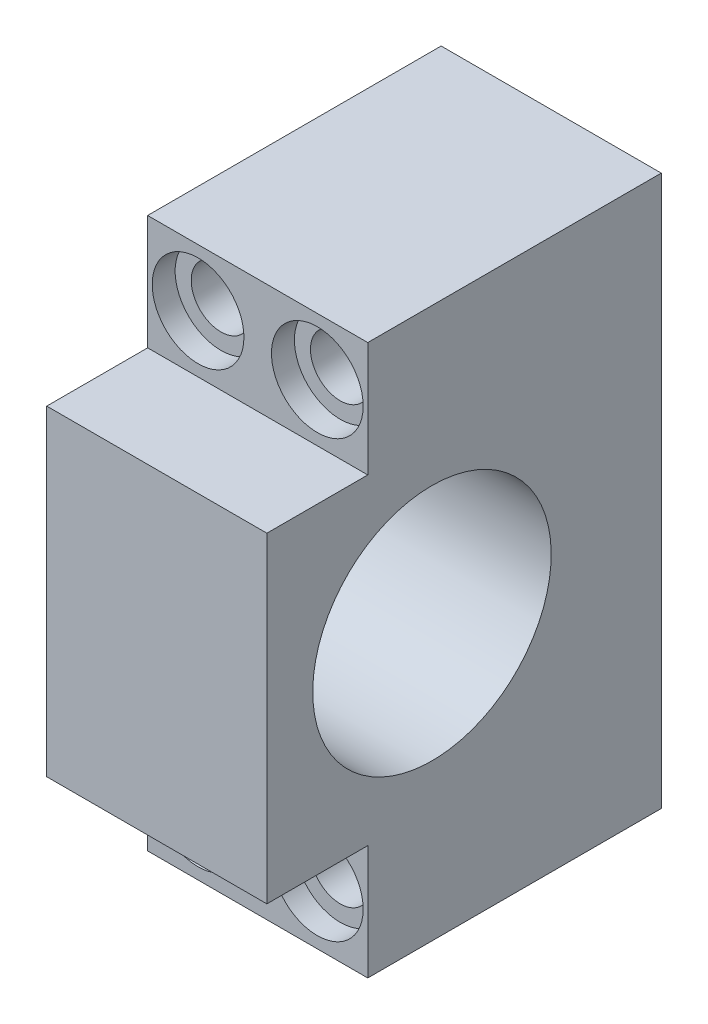
SolidWorks part; units mm, degrees
material "1.0037 (S235JR)"
ref_plane "Front Plane" through (0, 0, 0) normal (0, 0, 1) x (1, 0, 0)
ref_plane "Top Plane" through (0, 0, 0) normal (0, 1, 0) x (1, 0, 0)
ref_plane "Right Plane" through (0, 0, 0) normal (1, 0, 0) x (0, 0, -1)
sketch "Sketch1" plane through (0, 0, 0) normal (0, 0, 1) x (1, 0, 0)
  line L1 (-12, 30) -> (12, 30)
  line L2 (-12, 30) -> (-12, -30)
  line L3 (-12, -30) -> (12, -30)
  line L4 (12, 30) -> (12, -30)
  line L5 (-12, 30) -> (12, -30) construction
  line L6 (-12, -30) -> (12, 30) construction
  point P0 (0, 0)
  dimension "D1" = 24
  dimension "D2" = 60
extrude "Boss-Extrude1" add sketch "Sketch1" along normal blind 43
sketch "Sketch2" plane through (0, 0, 43) normal (0, 0, 1) x (1, 0, 0)
  line L0 (12, -30) -> (12, 30) construction
  line L1 (-12, -30) -> (12, -30)
  line L2 (-12, -30) -> (-12, -17.5)
  line L3 (-12, -17.5) -> (12, -17.5)
  line L4 (12, -30) -> (12, -17.5)
  line L6 (-12, 30) -> (12, 30)
  line L7 (-12, 30) -> (-12, 17.5)
  line L8 (-12, 17.5) -> (12, 17.5)
  line L9 (12, 30) -> (12, 17.5)
  dimension "D1" = 12.5
  dimension "D2" = 12.5
extrude "Cut-Extrude1" cut sketch "Sketch2" against normal blind 11
sketch "Sketch3" plane through (0, 0, 32) normal (0, 0, 1) x (1, 0, 0)
  line L0 (12, 30) -> (-12, 30) construction
  line L1 (-12, -30) -> (12, -30) construction
  line L2 (-12, 30) -> (-12, 17.5) construction
  line L3 (12, 17.5) -> (12, 30) construction
  circle A0 centre (-6.5, -23.75) radius 3.25
  circle A1 centre (6.5, -23.75) radius 3.25
  circle A2 centre (-6.5, 23.75) radius 3.25
  circle A3 centre (6.5, 23.75) radius 3.25
  dimension "D1" = 6.5
  dimension "D2" = 6.25
  dimension "D3" = 6.25
  dimension "D4" = 5.5
  dimension "D5" = 5.5
extrude "Cut-Extrude2" cut sketch "Sketch3" against normal through all
sketch "Sketch4" plane through (0, 0, 32) normal (0, 0, 1) x (1, 0, 0)
  circle A0 centre (-6.5, 23.75) radius 5
  circle A1 centre (6.5, 23.75) radius 5
  circle A2 centre (-6.5, -23.75) radius 5
  circle A3 centre (6.5, -23.75) radius 5
  dimension "D1" = 10
extrude "Cut-Extrude3" cut sketch "Sketch4" against normal blind 2.5
sketch "Sketch5" plane through (12, 0, 0) normal (1, 0, 0) x (0, 0, -1)
  circle A0 centre (-25, 0) radius 13
  dimension "D1" = 26
  dimension "D2" = 25
extrude "Cut-Extrude4" cut sketch "Sketch5" against normal through all
